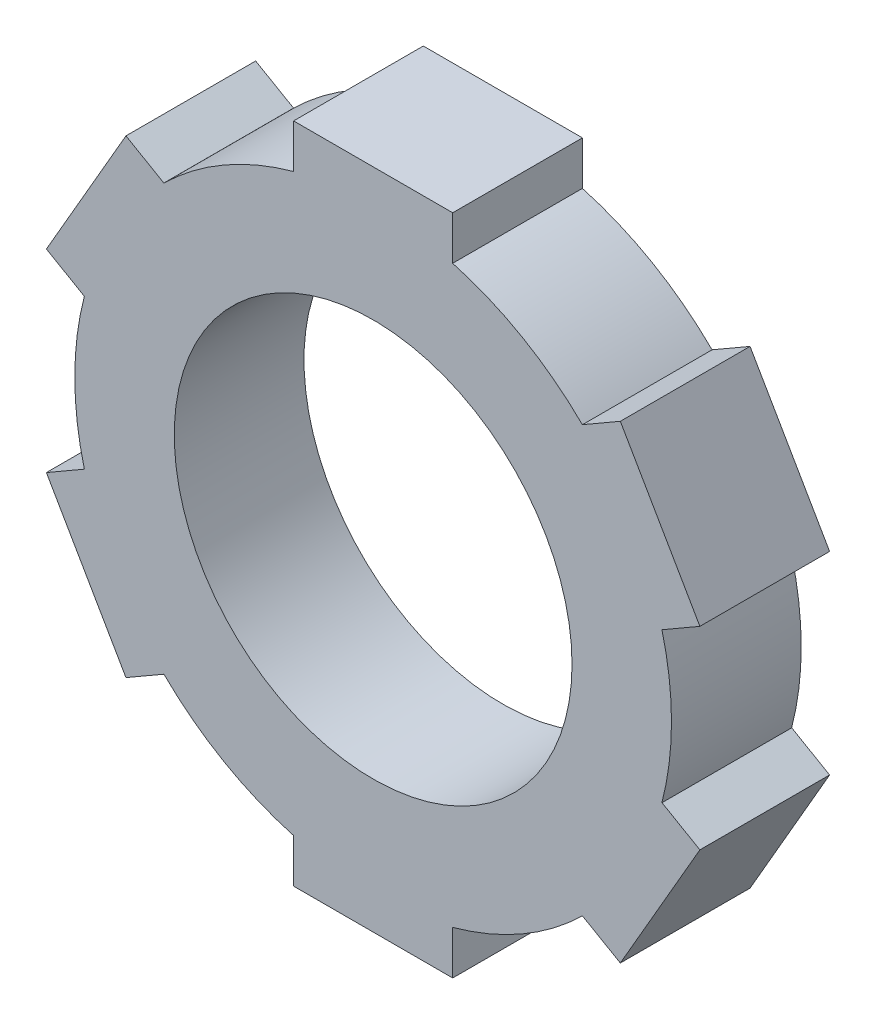
SolidWorks part; units mm, degrees
ref_plane "Front Plane" through (0, 0, 0) normal (0, 0, 1) x (1, 0, 0)
ref_plane "Top Plane" through (0, 0, 0) normal (0, 1, 0) x (1, 0, 0)
ref_plane "Right Plane" through (0, 0, 0) normal (1, 0, 0) x (0, 0, -1)
sketch "Sketch2" plane through (0, 0, 0) normal (0, 0, 1) x (1, 0, 0)
  circle A0 centre (0, 0) radius 11.5
  circle A1 centre (0, 0) radius 17.25
  dimension "D1" = 23
  dimension "D2" = 34.5
extrude "Boss-Extrude1" add sketch "Sketch2" along normal mid plane 7.5
sketch "Sketch3" plane through (0, 0, 0) normal (0, 0, 1) x (1, 0, 0)
  line L1 (4.6, 19.159) -> (-4.6, 19.159)
  line L2 (4.6, 19.159) -> (4.6, 16.629)
  line L3 (4.6, 16.629) -> (-4.6, 16.629)
  line L4 (-4.6, 19.159) -> (-4.6, 16.629)
  point P0 (0, 17.894)
  dimension "D1" = 9.2
  dimension "D2" = 2.53
  dimension "D3" = 19.159
extrude "Boss-Extrude2" add sketch "Sketch3" along normal up to surface (7.5 mm away) from surface at -3.75 up to face at (17.25, 0, 3.75) starting at face at (17.25, 0, -3.75)
pattern_circular "CirPattern1" count 6 over 360 about axis through (0, 0, 0) along (0, 0, 1) of "Boss-Extrude2"
